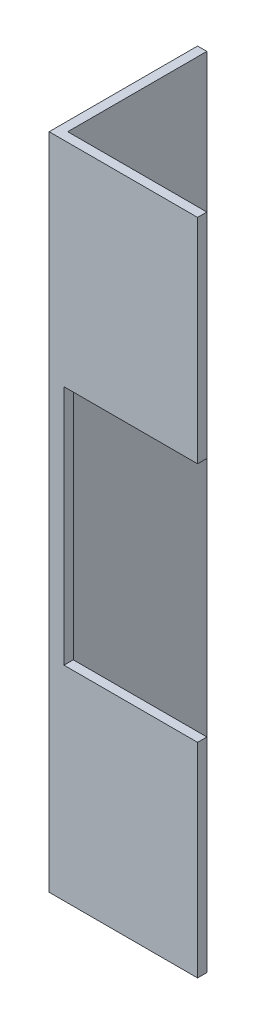
SolidWorks part; units mm, degrees
ref_plane "Front Plane" through (0, 0, 0) normal (0, 0, 1) x (1, 0, 0)
ref_plane "Top Plane" through (0, 0, 0) normal (0, 1, 0) x (1, 0, 0)
ref_plane "Right Plane" through (0, 0, 0) normal (1, 0, 0) x (0, 0, -1)
sketch "Sketch1" plane through (0, 0, 0) normal (0, 1, 0) x (1, 0, 0)
  line L0 (0, 0) -> (0, 25.4)
  line L1 (0, 25.4) -> (1.5875, 25.4)
  line L2 (1.5875, 25.4) -> (1.5875, 1.5875)
  line L3 (1.5875, 1.5875) -> (25.4, 1.5875)
  line L4 (25.4, 1.5875) -> (25.4, 0)
  line L5 (25.4, 0) -> (0, 0)
  dimension "D1" = 1.5875
  dimension "D2" = 25.4
extrude "Boss-Extrude1" add sketch "Sketch1" along normal blind 112.7125
sketch "Sketch4" plane through (0, 0, -1.5875) normal (0, 0, -1) x (-1, 0, 0)
  line L0 (-25.4, 112.7125) -> (-25.4, 0) construction
  line L1 (-25.4, 34.925) -> (-2.54, 34.925)
  line L2 (-25.4, 34.925) -> (-25.4, 76.2)
  line L3 (-25.4, 76.2) -> (-2.54, 76.2)
  line L4 (-2.54, 34.925) -> (-2.54, 76.2)
  line L5 (-25.4, 0) -> (-1.5875, 0) construction
  dimension "D1" = 34.925
  dimension "D2" = 41.275
  dimension "D3" = 22.86
extrude "Cut-Extrude1" cut sketch "Sketch4" against normal through all
